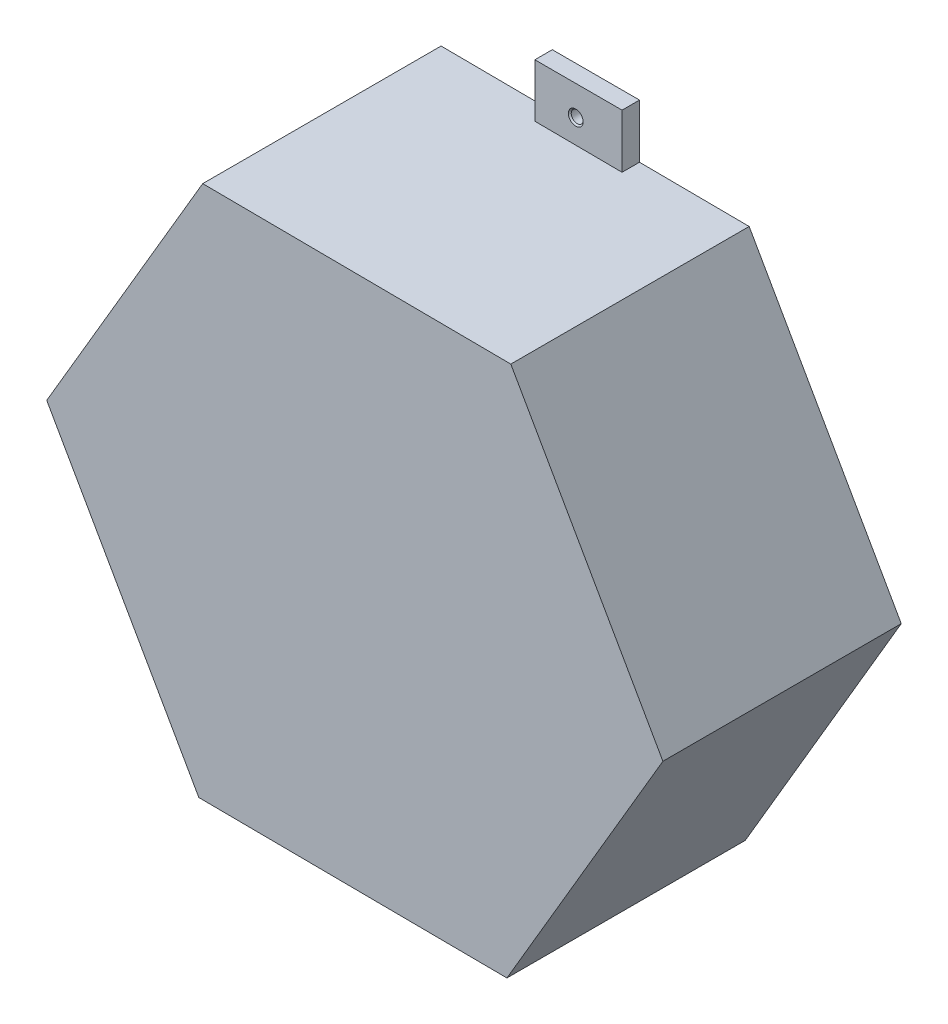
SolidWorks part; units mm, degrees
ref_plane "Front Plane" through (0, 0, 0) normal (0, 0, 1) x (1, 0, 0)
ref_plane "Top Plane" through (0, 0, 0) normal (0, 1, 0) x (1, 0, 0)
ref_plane "Right Plane" through (0, 0, 0) normal (1, 0, 0) x (0, 0, -1)
sketch "Sketch1" plane through (0, 0, 0) normal (0, 0, 1) x (1, 0, 0)
  line L1 (52.0783, 0) -> (26.0391, 45.1011)
  line L2 (26.0391, 45.1011) -> (-26.0391, 45.1011)
  line L3 (-26.0391, 45.1011) -> (-52.0783, 0)
  line L4 (-52.0783, 0) -> (-26.0391, -45.1011)
  line L5 (-26.0391, -45.1011) -> (26.0391, -45.1011)
  line L6 (26.0391, -45.1011) -> (52.0783, 0)
  circle A0 centre (0, 0) radius 44
  dimension "D1" = 88
extrude "Boss-Extrude4" add sketch "Sketch1" along normal blind 40 and the other way blind 1 contours L1 L2 L3 L4 L5 L6
sketch "Sketch10" plane through (0, 0, -1) normal (0, 0, -1) x (-1, 0, 0)
  circle A0 centre (0, 0) radius 44
  dimension "D1" = 88
extrude "Cut-Extrude3" cut sketch "Sketch10" against normal blind 38
sketch "Sketch11" plane through (0, 0, -1) normal (0, 0, -1) x (-1, 0, 0)
  line L0 (-26.0391, 45.1011) -> (26.0391, 45.1011) construction
  line L1 (-7.968, 45.1011) -> (7.032, 45.1011)
  line L2 (-7.968, 45.1011) -> (-7.968, 55.1011)
  line L3 (-7.968, 55.1011) -> (7.032, 55.1011)
  line L4 (7.032, 45.1011) -> (7.032, 55.1011)
  line L5 (26.0391, -45.1011) -> (-26.0391, -45.1011) construction
  line L6 (-7.968, -45.1011) -> (7.032, -45.1011)
  line L7 (-7.968, -45.1011) -> (-7.968, -55.1011)
  line L8 (-7.968, -55.1011) -> (7.032, -55.1011)
  line L9 (7.032, -45.1011) -> (7.032, -55.1011)
  dimension "D1" = 15
  dimension "D2" = 15
  dimension "D3" = 10
  dimension "D4" = 10
extrude "Boss-Extrude5" add sketch "Sketch11" against normal blind 3
hole_wizard "M2.5x0.45 Tapped Hole3" positions "Sketch14" profile "Sketch15" tap size "M2.5x0.45" standard "ANSI Metric" end condition through all
sketch "Sketch14" plane through (0, 0, 2) normal (0, 0, 1) x (1, 0, 0)
  point P0 (0, 50)
  point P2 (0, -50)
  dimension "D1" = 50
  dimension "D2" = 50
sketch "Sketch15" plane through (0, 50, 2) normal (1, 0, 0) x (0, -1, 0)
  line L0 (0, 0) -> (0, 3)
  line L1 (0, 3) -> (1.025, 3)
  line L2 (1.025, 3) -> (1.025, 0.25)
  line L3 (1.025, 0.25) -> (1.275, 0)
  line L5 (1.275, 0) -> (0, 0)
  line L6 (-1.025, 0.25) -> (-1.275, 0) construction
  line L11 (0, -6.35) -> (0, 107.95) construction
  dimension "Thru Tap Drill Dia." = 2.05
  dimension "Thru Tap Drill Depth" = 3
  dimension "Near C'Sink Dia." = 2.55
  dimension "Near C'Sink Angle" = 90
cosmetic thread "Hole Thread5" parameters "D2"=2.5
cosmetic thread "Hole Thread6" parameters "D2"=2.5
sketch "Sketch16" plane through (0, 0, 40) normal (0, 0, 1) x (1, 0, 0)
  line L1 (-52.9936, 0.3857) -> (-26.8308, -45.701)
  line L2 (-26.8308, -45.701) -> (26.1628, -46.0867)
  line L3 (26.1628, -46.0867) -> (52.9936, -0.3857)
  line L4 (52.9936, -0.3857) -> (26.8308, 45.701)
  line L5 (26.8308, 45.701) -> (-26.1628, 46.0867)
  line L6 (-26.1628, 46.0867) -> (-52.9936, 0.3857)
  circle A0 centre (0, 0) radius 45.895 construction
extrude "Boss-Extrude6" add sketch "Sketch16" against normal blind 41
sketch "Sketch17" plane through (0, 0, -1) normal (0, 0, -1) x (-1, 0, 0)
  circle A0 centre (0, 0) radius 44
  dimension "D1" = 88
extrude "Cut-Extrude4" cut sketch "Sketch17" against normal blind 38
